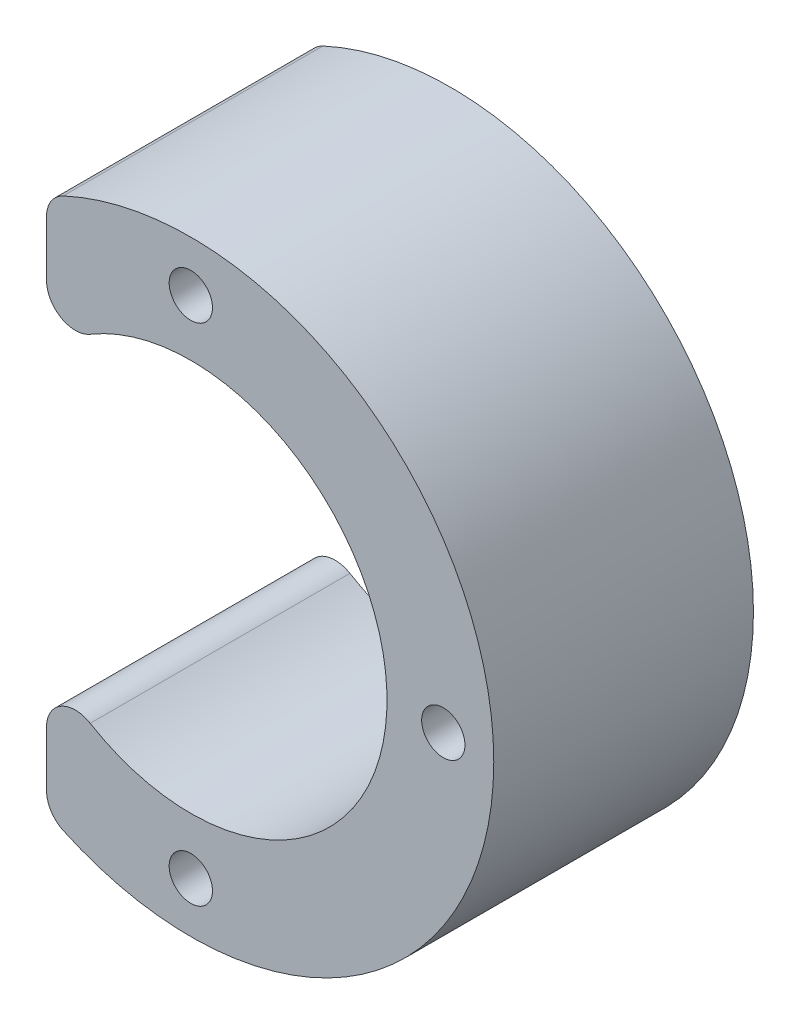
SolidWorks part; units mm, degrees
ref_plane "前视基准面" through (0, 0, 0) normal (0, 0, 1) x (1, 0, 0)
ref_plane "上视基准面" through (0, 0, 0) normal (0, 1, 0) x (1, 0, 0)
ref_plane "右视基准面" through (0, 0, 0) normal (1, 0, 0) x (0, 0, -1)
sketch "草图1" plane through (0, 0, 0) normal (0, 0, 1) x (1, 0, 0)
  circle A0 centre (0, 0) radius 21
  dimension "D1" = 42
extrude "凸台-拉伸1" add sketch "草图1" along normal blind 18
sketch "草图2" plane through (0, 0, 18) normal (0, 0, 1) x (1, 0, 0)
  circle A0 centre (-17.5, 0) radius 1.5
  circle A4 centre (0, 0) radius 13.6
  circle A8 centre (0, 17.5) radius 1.5
  circle A9 centre (17.5, 0) radius 1.5
  circle A10 centre (0, -17.5) radius 1.5
  dimension "D2" = 3
  dimension "D4" = 27.2
  dimension "D1" = 17.5
  dimension "D3" = 4
extrude "切除-拉伸1" cut sketch "草图2" against normal blind 25
sketch "草图4" plane through (0, 0, 0) normal (0, 0, -1) x (-1, 0, 0)
  line L0 (10, 18.4662) -> (10, -19.3397)
  line L1 (10, -19.3397) -> (24.1556, -19.3397)
  line L2 (24.1556, -19.3397) -> (24.1556, 18.4662)
  line L3 (24.1556, 18.4662) -> (10, 18.4662)
  circle A0 centre (0, 0) radius 21 construction
  dimension "D1" = 10
extrude "切除-拉伸2" cut sketch "草图4" against normal blind 25
fillet "圆角1" radius 2 4 edges at (-10, -18.4662, 9) (-10, 18.4662, 9) (-10, 9.2174, 9) (-10, -9.2174, 9)
